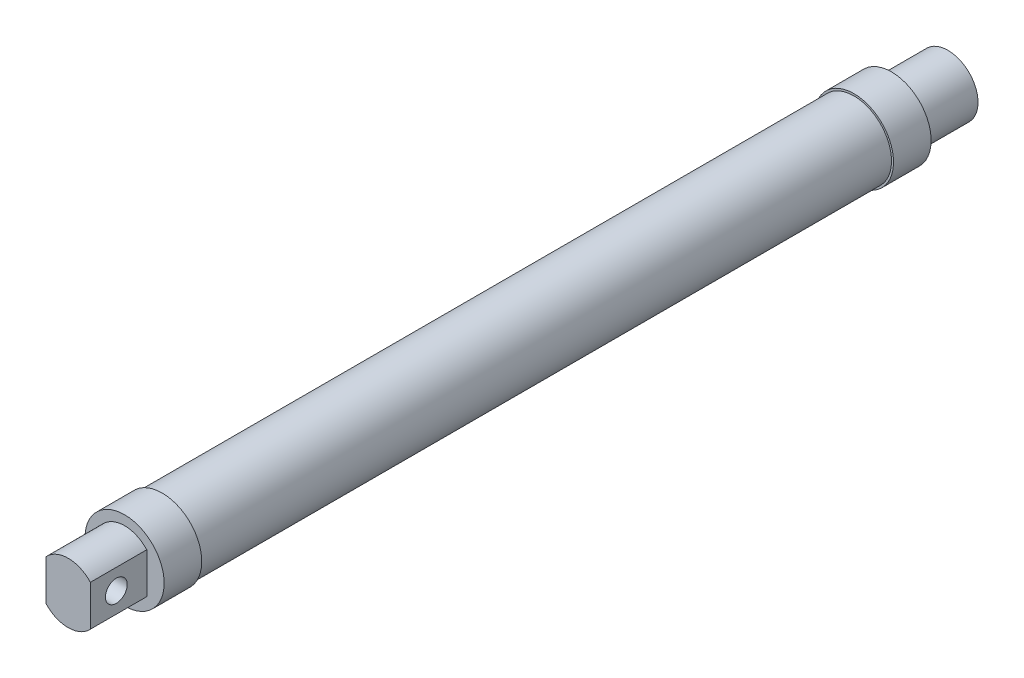
SolidWorks part; units mm, degrees
ref_plane "Спереди" through (0, 0, 0) normal (0, 0, 1) x (1, 0, 0)
ref_plane "Сверху" through (0, 0, 0) normal (0, 1, 0) x (1, 0, 0)
ref_plane "Справа" through (0, 0, 0) normal (1, 0, 0) x (0, 0, -1)
sketch "Sketch2" plane through (0, 0, 0) normal (1, 0, 0) x (0, 0, -1)
  line L0 (116.1733, 10.525) -> (116.1733, 8)
  line L2 (-102.8267, 8) -> (-87.8267, 8)
  line L3 (-87.8267, 8) -> (-87.8267, 10.525)
  line L4 (-87.8267, 10.525) -> (-77.8267, 10.525)
  line L5 (-77.8267, 10.525) -> (-77.8267, 10)
  line L6 (-77.8267, 10) -> (106.1733, 10)
  line L7 (106.1733, 10) -> (106.1733, 10.525)
  line L8 (106.1733, 10.525) -> (116.1733, 10.525)
  line L12 (116.1733, 8) -> (131.1733, 8)
  line L13 (131.1733, 8) -> (131.1733, 0)
  line L14 (131.1733, 0) -> (-102.8267, 0)
  line L15 (-102.8267, 0) -> (-102.8267, 8)
  dimension "D1" = 8
  dimension "D2" = 15
  dimension "D3" = 10
  dimension "D4" = 184
  dimension "D5" = 10
  dimension "D6" = 15
  dimension "D7" = 10.525
  dimension "D8" = 10.525
  dimension "D9" = 10
revolve "Revolve1" add sketch "Sketch2" angle 360 about L14
sketch "Sketch3" plane through (0, 0, 102.8267) normal (0, 0, 1) x (1, 0, 0)
  line L0 (-5.9, 5.4028) -> (-5.9, -5.4028)
  line L1 (5.9, -5.4028) -> (5.9, 5.4028)
  line L2 (5.9, 0) -> (-5.9, 0) construction
  circle A0 centre (0, 0) radius 8 construction
  arc A1 (-5.9, -5.4028) -> (-5.9, 5.4028) centre (0, 0) cw
  arc A2 (5.9, 5.4028) -> (5.9, -5.4028) centre (0, 0) cw
  point P12 (0, 0)
  dimension "D1" = 11.8
extrude "Cut-Extrude1" cut sketch "Sketch3" against normal up to surface (15 mm away) up to face at (0, 8, 87.8267)
sketch "Sketch4" plane through (5.9, 0, 0) normal (1, 0, 0) x (0, 0, -1)
  line L0 (-102.8267, 0) -> (-87.8267, 0) construction
  line L1 (-102.8267, 5.4028) -> (-102.8267, -5.4028) construction
  line L2 (-87.8267, -5.4028) -> (-87.8267, 5.4028) construction
  circle A0 centre (-95.9267, 0) radius 2.9
  point P8 (-98.8267, 0)
  dimension "D1" = 5.8
  dimension "D2" = 4
extrude "Cut-Extrude2" cut sketch "Sketch4" against normal through all
sketch "Sketch5" plane through (0, 0, -131.1733) normal (0, 0, -1) x (-1, 0, 0)
  circle A0 centre (0, 0) radius 3
  dimension "D1" = 6
extrude "Cut-Extrude3" cut sketch "Sketch5" against normal blind 180
